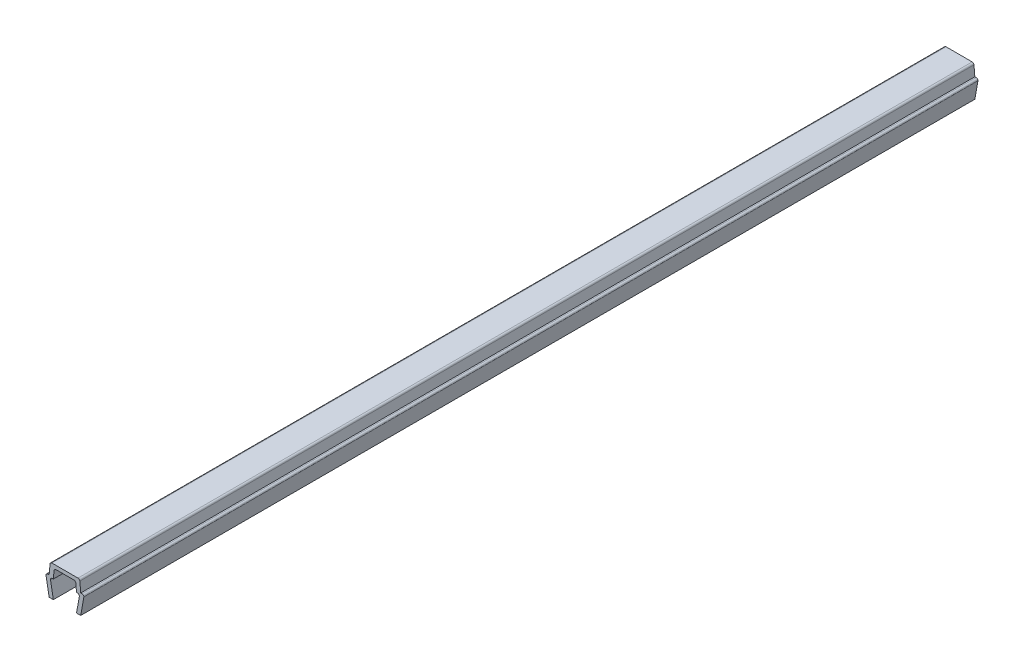
SolidWorks part; units mm, degrees
ref_plane "Front Plane" through (0, 0, 0) normal (0, 0, 1) x (1, 0, 0)
ref_plane "Top Plane" through (0, 0, 0) normal (0, 1, 0) x (1, 0, 0)
ref_plane "Right Plane" through (0, 0, 0) normal (1, 0, 0) x (0, 0, -1)
ref_plane "Plane1" through (0, 0, 0) normal (0, 0, 1) x (1, 0, 0)
sketch "Sketch1" plane through (0, 0, 0) normal (0, 0, 1) x (1, 0, 0)
  line L0 (-3.6, 3.35) -> (-3, 0)
  line L1 (-3, 0) -> (-2.2, 0)
  line L2 (-2.2, 0) -> (-2.7352, 2.9883)
  line L3 (-2.3907, 3.4) -> (-2.2, 3.4)
  line L4 (-2.2, 3.4) -> (-2.0705, 4.8805)
  line L5 (-1.7218, 5.2) -> (1.7218, 5.2)
  line L6 (2.0705, 4.8805) -> (2.2, 3.4)
  line L7 (2.2, 3.4) -> (2.3907, 3.4)
  line L8 (2.7352, 2.9883) -> (2.2, 0)
  line L9 (2.2, 0) -> (3, 0)
  line L10 (3, 0) -> (3.6, 3.35)
  line L11 (3.25, 3.7) -> (3, 3.7)
  line L12 (3, 3.7) -> (2.8355, 5.5805)
  line L13 (2.4868, 5.9) -> (-2.4868, 5.9)
  line L14 (-2.8355, 5.5805) -> (-3, 3.7)
  line L15 (-3, 3.7) -> (-3.25, 3.7)
  arc A0 (-2.7352, 2.9883) -> (-2.3907, 3.4) centre (-2.3907, 3.05) cw
  arc A1 (-2.0705, 4.8805) -> (-1.7218, 5.2) centre (-1.7218, 4.85) cw
  arc A2 (1.7218, 5.2) -> (2.0705, 4.8805) centre (1.7218, 4.85) cw
  arc A3 (2.3907, 3.4) -> (2.7352, 2.9883) centre (2.3907, 3.05) cw
  arc A4 (3.6, 3.35) -> (3.25, 3.7) centre (3.25, 3.35) ccw
  arc A5 (2.8355, 5.5805) -> (2.4868, 5.9) centre (2.4868, 5.55) ccw
  arc A6 (-2.4868, 5.9) -> (-2.8355, 5.5805) centre (-2.4868, 5.55) ccw
  arc A7 (-3.25, 3.7) -> (-3.6, 3.35) centre (-3.25, 3.35) ccw
extrude "Boss-Extrude1" add sketch "Sketch1" against normal mid plane 170
